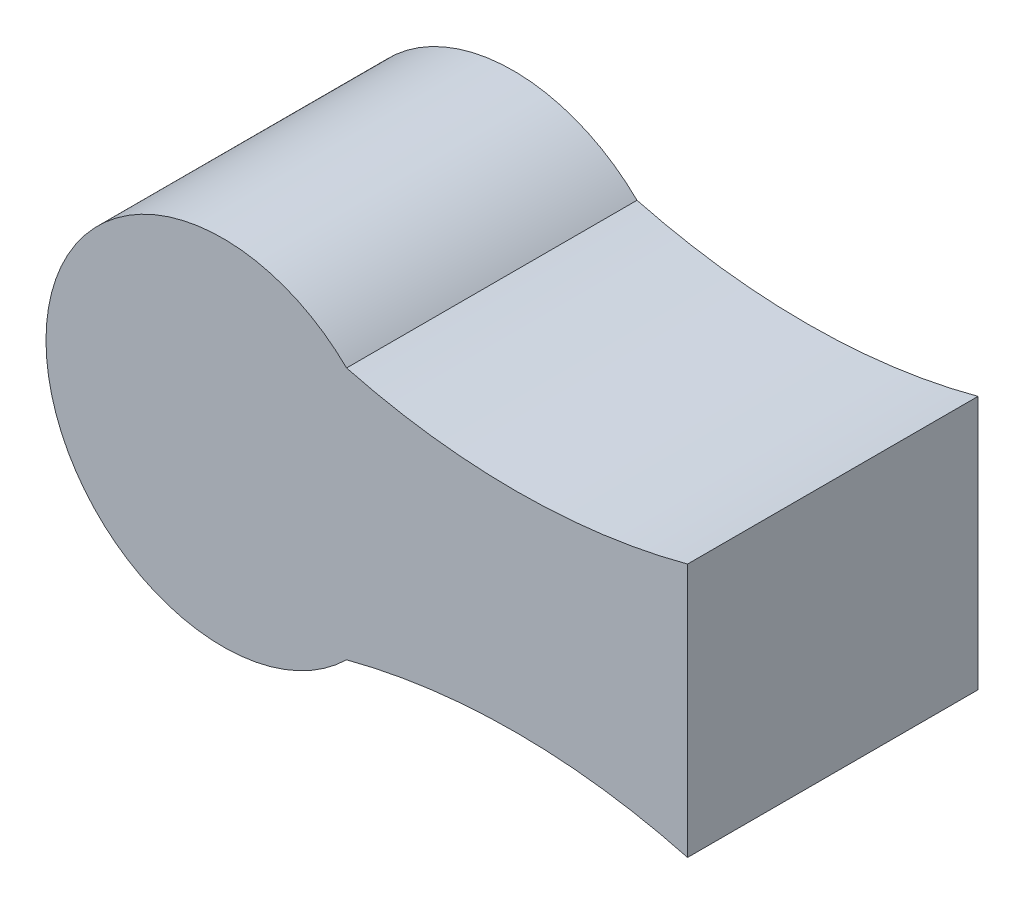
SolidWorks part; units mm, degrees
ref_plane "Płaszczyzna przednia" through (0, 0, 0) normal (0, 0, 1) x (1, 0, 0)
ref_plane "Płaszczyzna górna" through (0, 0, 0) normal (0, 1, 0) x (1, 0, 0)
ref_plane "Płaszczyzna prawa" through (0, 0, 0) normal (1, 0, 0) x (0, 0, -1)
sketch "Szkic2" plane through (0, 0, 0) normal (0, 0, 1) x (1, 0, 0)
  line L0 (175.4927, 10.8317) -> (-22.3982, 10.8317) construction
  line L1 (175.4927, -24.1683) -> (175.4927, 45.8317)
  line L2 (-22.3982, 10.8317) -> (202.9629, 10.8317) construction
  arc A0 (81.57, 45.64) -> (81.57, -23.9767) centre (47.4927, 10.8317) ccw
  arc A3 (175.4927, 45.8317) -> (81.57, 45.64) centre (128.17, 222.8107) cw
  arc A4 (175.4927, -24.1683) -> (81.57, -23.9767) centre (128.17, -201.1474) ccw
  point P7 (175.4927, 10.8317)
extrude "Dodanie-wyciągnięcie2" add sketch "Szkic2" along normal blind 80
sketch "Szkic3" plane through (0, 0, 0) normal (0, 0, -1) x (-1, 0, 0)
  circle A1 centre (-47.4927, 10.8317) radius 48.7122
sketch "Szkic4" plane through (175.4927, 0, 0) normal (1, 0, 0) x (0, 0, -1)
  circle A0 centre (-40, 10.8317) radius 31.5492
ref_plane "Płaszczyzna1" through (0, 0, 40) normal (0, 0, 1) x (1, 0, 0)
sketch "Szkic5" plane through (0, 0, 40) normal (0, 0, 1) x (1, 0, 0)
  line L0 (-1.2195, 10.8317) -> (175.4927, 10.8317) construction
  line L1 (175.4927, -20.7175) -> (175.4927, 42.3808) construction
  line L3 (117.3985, -6.9683) -> (152.9985, -6.9683)
  line L4 (117.3985, -6.9683) -> (117.3985, 28.6317)
  line L5 (117.3985, 28.6317) -> (152.9985, 28.6317)
  line L6 (152.9985, -6.9683) -> (152.9985, 28.6317)
  line L7 (117.3985, -6.9683) -> (152.9985, 28.6317) construction
  line L8 (117.3985, 28.6317) -> (152.9985, -6.9683) construction
  circle A0 centre (47.4927, 10.8317) radius 48.7122 construction
  point P6 (135.1985, 10.8317)
  dimension "D1" = 35.6
  dimension "D2" = 35.6
extrude "Wytnij-wyciągnięcie1" cut sketch "Szkic5" against normal blind 17.8 and the other way blind 17.8
